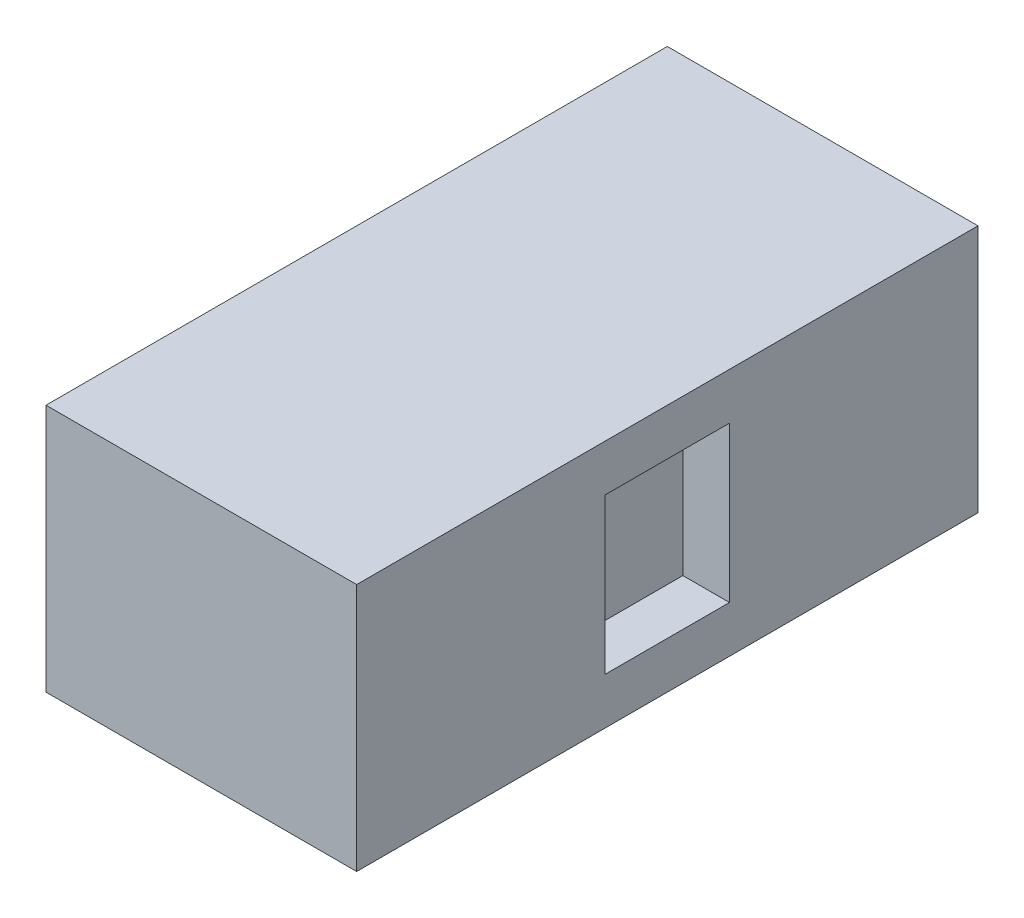
SolidWorks part; units mm, degrees
ref_plane "Front Plane" through (0, 0, 0) normal (0, 0, 1) x (1, 0, 0)
ref_plane "Top Plane" through (0, 0, 0) normal (0, 1, 0) x (1, 0, 0)
ref_plane "Right Plane" through (0, 0, 0) normal (1, 0, 0) x (0, 0, -1)
sketch "Sketch1" plane through (0, 0, 0) normal (0, 1, 0) x (1, 0, 0)
  line L1 (10, -20) -> (-10, -20)
  line L2 (10, -20) -> (10, 20)
  line L3 (10, 20) -> (-10, 20)
  line L4 (-10, -20) -> (-10, 20)
  line L5 (10, -20) -> (-10, 20) construction
  line L6 (10, 20) -> (-10, -20) construction
  point P0 (0, 0)
  dimension "D1" = 20
  dimension "D2" = 40
extrude "Boss-Extrude1" add sketch "Sketch1" along normal blind 3
sketch "Sketch2" plane through (0, 3, 0) normal (0, 1, 0) x (1, 0, 0)
  line L0 (-10, 0) -> (10, 0) construction
  line L1 (10, -20) -> (-10, -20)
  line L2 (10, -20) -> (10, 20)
  line L3 (10, 20) -> (-10, 20)
  line L4 (-10, -20) -> (-10, 20)
  line L5 (10, -20) -> (-10, 20) construction
  line L6 (10, 20) -> (-10, -20) construction
  line L7 (10, -4) -> (7, -4)
  line L8 (7, -4) -> (7, 0)
  line L9 (7, 4) -> (7, 0)
  line L10 (10, 4) -> (7, 4)
  point P0 (0, 0)
  line M8 (-10, 20) -> (-10, -20)
  line M9 (-10, -20) -> (10, -20)
  line M10 (10, -20) -> (10, 20)
  line M11 (10, 20) -> (-10, 20)
  dimension "D1" = 4
  dimension "D2" = 3
extrude "Boss-Extrude2" add sketch "Sketch2" along normal blind 10 contours L10 L7 L8 L9 M10 M11 M8 M9
ref_plane "Plane1" through (7, 13, -4) normal (0, 0, -1) x (-1, 0, 0)
sketch "Sketch4" plane through (0, 13, 0) normal (0, 1, 0) x (1, 0, 0)
  line L1 (-10, 20) -> (10, 20)
  line L2 (-10, 20) -> (-10, -20)
  line L3 (-10, -20) -> (10, -20)
  line L4 (10, 20) -> (10, -20)
extrude "Boss-Extrude3" add sketch "Sketch4" along normal blind 3
